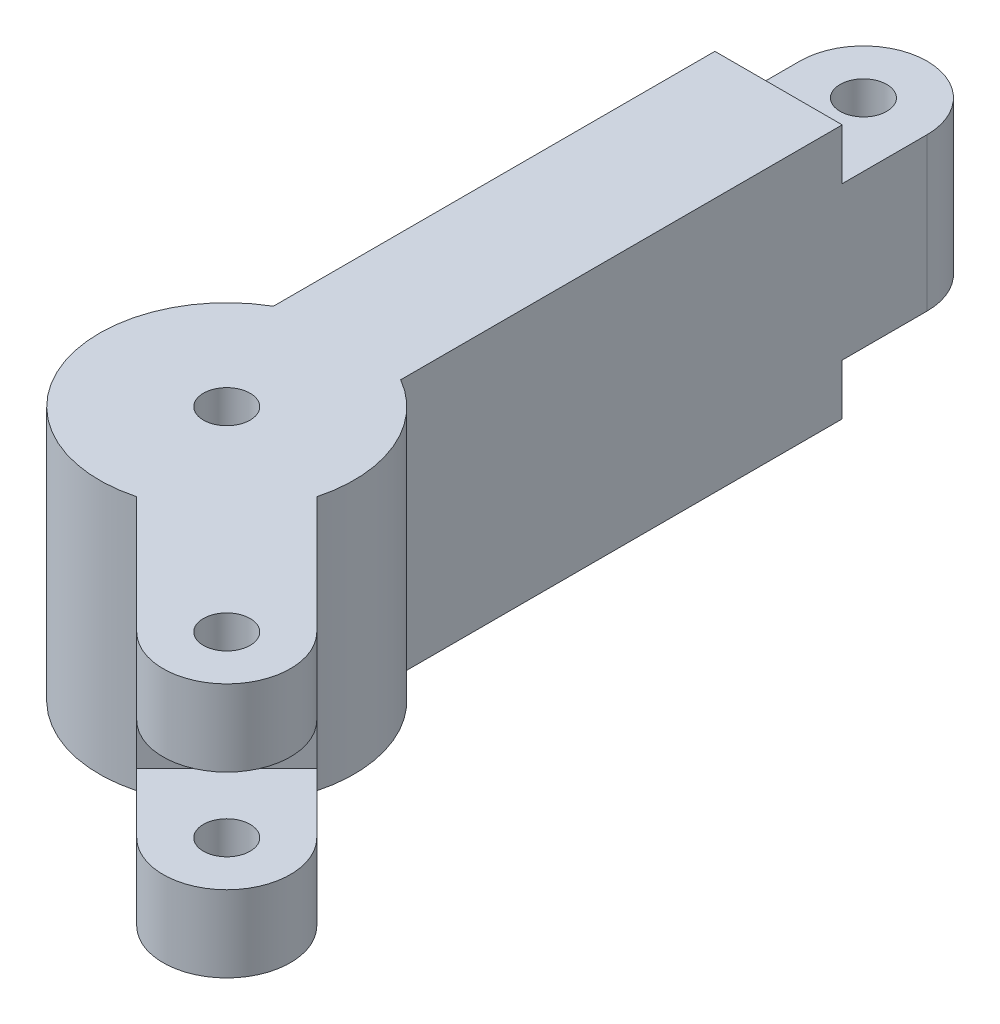
SolidWorks part; units mm, degrees
ref_plane "Front Plane" through (0, 0, 0) normal (0, 0, 1) x (1, 0, 0)
ref_plane "Top Plane" through (0, 0, 0) normal (0, 1, 0) x (1, 0, 0)
ref_plane "Right Plane" through (0, 0, 0) normal (1, 0, 0) x (0, 0, -1)
sketch "Sketch1" plane through (0, 0, 0) normal (0, 1, 0) x (1, 0, 0)
  line L0 (0, 0) -> (0, 75)
  line L1 (0, 0) -> (22.981, -22.981)
  line L2 (0, 75) -> (0, 0) construction
  line L3 (7.5, 75) -> (7.5, 0)
  line L4 (-7.5, 75) -> (-7.5, 0)
  line L5 (0, 0) -> (22.981, -22.981) construction
  line L6 (5.3033, 5.3033) -> (28.2843, -17.6777)
  line L7 (-5.3033, -5.3033) -> (17.6777, -28.2843)
  circle A0 centre (0, 75) radius 2.75
  circle A1 centre (0, 0) radius 2.75
  circle A2 centre (22.981, -22.981) radius 2.75
  arc A3 (7.5, 75) -> (-7.5, 75) centre (0, 75) ccw
  arc A4 (-7.5, 0) -> (7.5, 0) centre (0, 0) ccw
  arc A5 (5.3033, 5.3033) -> (-5.3033, -5.3033) centre (0, 0) ccw
  arc A6 (17.6777, -28.2843) -> (28.2843, -17.6777) centre (22.981, -22.981) ccw
  circle A7 centre (0, 0) radius 15
  point P7 (0, 37.5)
  point P12 (11.4905, -11.4905)
extrude "Boss-Extrude1" add sketch "Sketch1" along normal blind 30
sketch "Sketch2" plane through (7.5, 0, 0) normal (1, 0, 0) x (0, 0, -1)
  line L0 (75, 15) -> (75, 6)
  line L1 (75, 30) -> (75, 0) construction
  line L2 (75, 15) -> (75, 24)
  line L3 (75, 24) -> (88.3404, 24)
  line L4 (88.3404, 24) -> (88.3404, 6)
  line L5 (88.3404, 6) -> (75, 6)
  line L6 (75, 6) -> (65, 6)
  line L7 (65, 6) -> (65, 24)
  line L8 (65, 24) -> (75, 24)
  line L10 (88.3404, 24) -> (65, 24)
  line L11 (88.3404, 24) -> (88.3404, 42.2228)
  line L12 (88.3404, 42.2228) -> (65, 42.2228)
  line L13 (65, 24) -> (65, 42.2228)
  line L14 (88.3404, 6) -> (65, 6)
  line L15 (88.3404, 6) -> (88.3404, -8.6827)
  line L16 (88.3404, -8.6827) -> (65, -8.6827)
  line L17 (65, 6) -> (65, -8.6827)
  line M2 (12.9904, 0) -> (75, 0)
  line M3 (75, 0) -> (75, 30)
  line M4 (75, 30) -> (12.9904, 30)
extrude "Cut-Extrude1" cut sketch "Sketch2" against normal blind 55 contours L13 L3 L11 L12 M4 M3 | L17 L16 L15 L5 M2 M3 | L6 L17 M2 M3 | L13 L8 M3 M4
sketch "Sketch3" plane through (5.3033, 0, -5.3033) normal (0.7071, 0, -0.7071) x (-0.7071, 0, -0.7071)
  line L0 (-32.5, 15) -> (-32.5, 9)
  line L1 (-32.5, 30) -> (-32.5, 0) construction
  line L2 (-32.5, 9) -> (-50.5802, 9)
  line L3 (-50.5802, 9) -> (-50.5802, 21)
  line L4 (-50.5802, 21) -> (-32.5, 21)
  line L5 (-32.5, 21) -> (-22.5, 21)
  line L6 (-22.5, 21) -> (-22.5, 9)
  line L7 (-22.5, 9) -> (-32.5, 9)
  line M4 (-32.5, 30) -> (-32.5, 0)
extrude "Cut-Extrude2" cut sketch "Sketch3" against normal blind 17 contours L7 L6 L5 M4 | L4 L3 L2 M4
